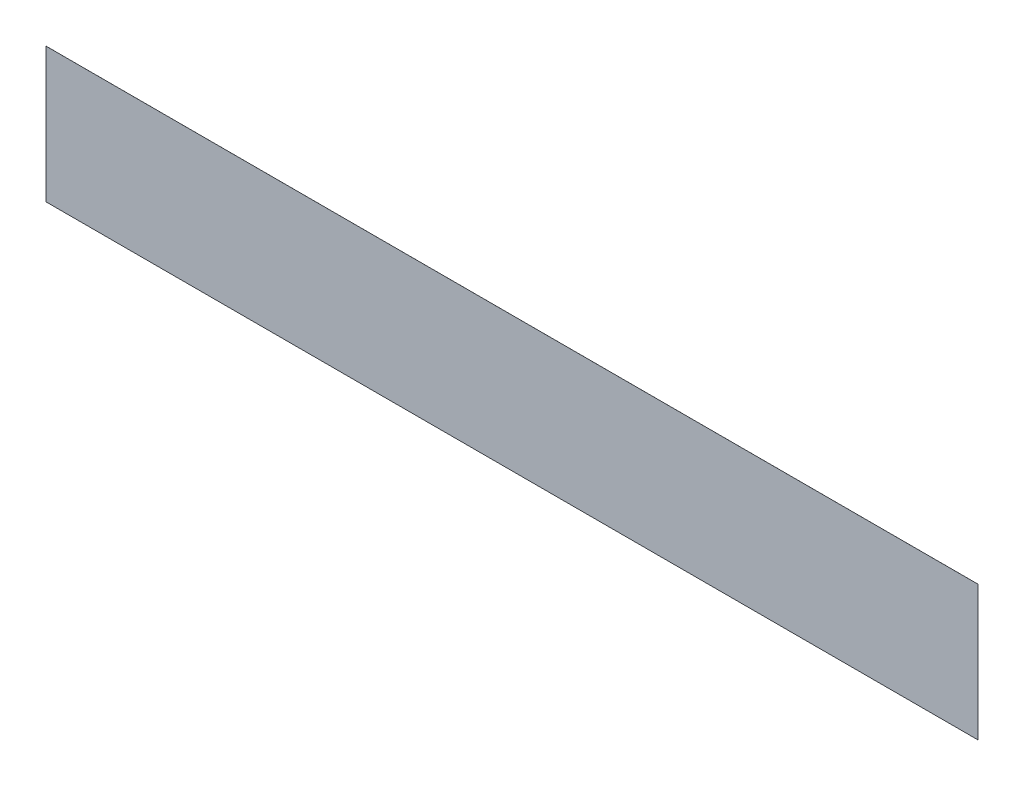
SolidWorks part; units mm, degrees
ref_plane "Alzado" through (0, 0, 0) normal (0, 0, 1) x (1, 0, 0)
ref_plane "Planta" through (0, 0, 0) normal (0, 1, 0) x (1, 0, 0)
ref_plane "Vista lateral" through (0, 0, 0) normal (1, 0, 0) x (0, 0, -1)
sketch "Croquis1" plane through (0, 0, 0) normal (0, 0, 1) x (1, 0, 0)
  line L1 (-19000, 2750) -> (19000, 2750)
  line L2 (-19000, 2750) -> (-19000, -2750)
  line L3 (-19000, -2750) -> (19000, -2750)
  line L4 (19000, 2750) -> (19000, -2750)
  line L5 (-19000, 2750) -> (19000, -2750) construction
  line L6 (-19000, -2750) -> (19000, 2750) construction
  point P0 (0, 0)
  dimension "D1" = 38000
  dimension "D2" = 5500
extrude "Saliente-Extruir1" add sketch "Croquis1" along normal blind 1
